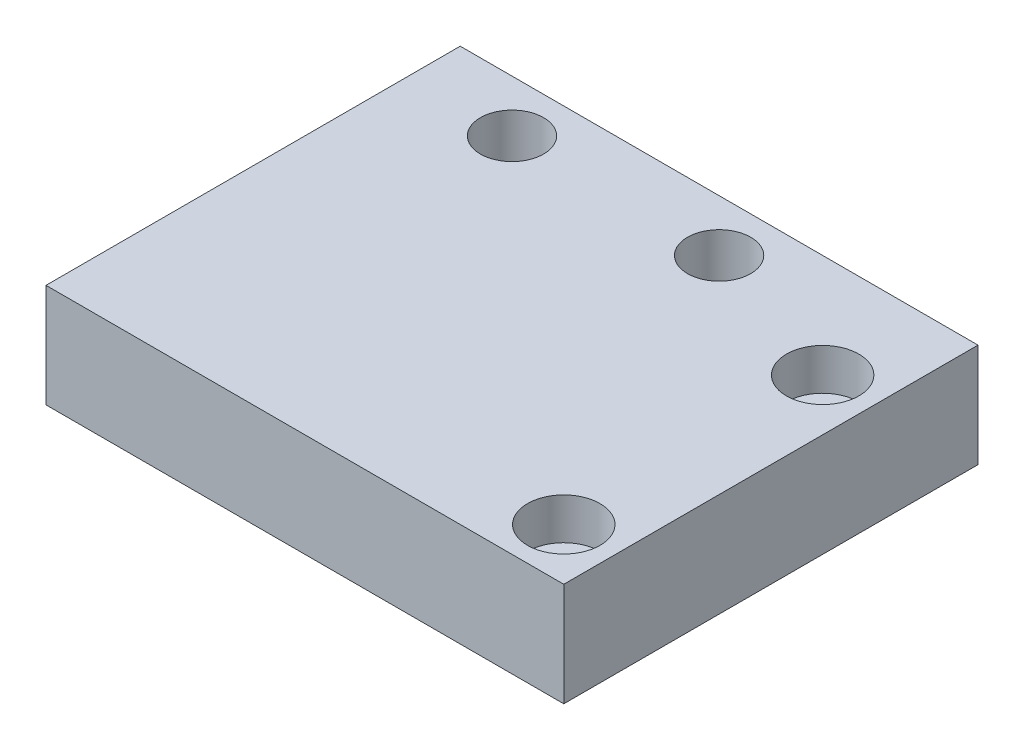
SolidWorks part; units mm, degrees
ref_plane "Front Plane" through (0, 0, 0) normal (0, 0, 1) x (1, 0, 0)
ref_plane "Top Plane" through (0, 0, 0) normal (0, 1, 0) x (1, 0, 0)
ref_plane "Right Plane" through (0, 0, 0) normal (1, 0, 0) x (0, 0, -1)
sketch "Sketch1" plane through (0, 0, 0) normal (0, 1, 0) x (1, 0, 0)
  line L1 (-25, 20) -> (25, 20)
  line L2 (-25, 20) -> (-25, -20)
  line L3 (-25, -20) -> (25, -20)
  line L4 (25, 20) -> (25, -20)
  line L5 (-25, 20) -> (25, -20) construction
  line L6 (-25, -20) -> (25, 20) construction
  point P0 (0, 0)
  dimension "D1" = 50
  dimension "D2" = 40
extrude "Boss-Extrude1" add sketch "Sketch1" along normal blind 10
sketch "Sketch2" plane through (0, 10, 0) normal (0, 1, 0) x (1, 0, 0)
  line L0 (25, 20) -> (-25, 20) construction
  line L1 (25, -20) -> (25, 20) construction
  circle A0 centre (20, 10) radius 2.05
  dimension "D1" = 4.1
  dimension "D2" = 10
  dimension "D3" = 5
extrude "Cut-Extrude1" cut sketch "Sketch2" against normal up to surface (10 mm away) up to face at (0, 0, 0)
sketch "Sketch4" plane through (0, 10, 0) normal (0, 1, 0) x (1, 0, 0)
  line L0 (25, 20) -> (-25, 20) construction
  line L2 (-25, 20) -> (-25, -20) construction
  circle A0 centre (-15, 15) radius 3.05
  circle A1 centre (5, 15) radius 3.05
  dimension "D1" = 6.1
  dimension "D4" = 6.1
  dimension "D2" = 5
  dimension "D3" = 10
  dimension "D5" = 5
  dimension "D6" = 20
extrude "Cut-Extrude2" cut sketch "Sketch4" against normal up to surface (10 mm away) up to face at (20, 0, -7.95)
sketch "Sketch5" plane through (0, 10, 0) normal (0, 1, 0) x (1, 0, 0)
  line L0 (25, -20) -> (25, 20) construction
  line L1 (-25, -20) -> (25, -20) construction
  circle A0 centre (20, -15) radius 2
  dimension "D1" = 4
  dimension "D2" = 5
  dimension "D3" = 5
extrude "Cut-Extrude3" cut sketch "Sketch5" against normal up to surface (10 mm away) up to face at (-15, 0, -11.95)
sketch "Sketch6" plane through (0, 10, 0) normal (0, 1, 0) x (1, 0, 0)
  circle A0 centre (20, 10) radius 3.5
  dimension "D1" = 7
extrude "Cut-Extrude4" cut sketch "Sketch6" against normal blind 4
sketch "Sketch7" plane through (0, 10, 0) normal (0, 1, 0) x (1, 0, 0)
  circle A0 centre (20, -15) radius 3.5
  dimension "D1" = 7
extrude "Cut-Extrude5" cut sketch "Sketch7" against normal blind 4
